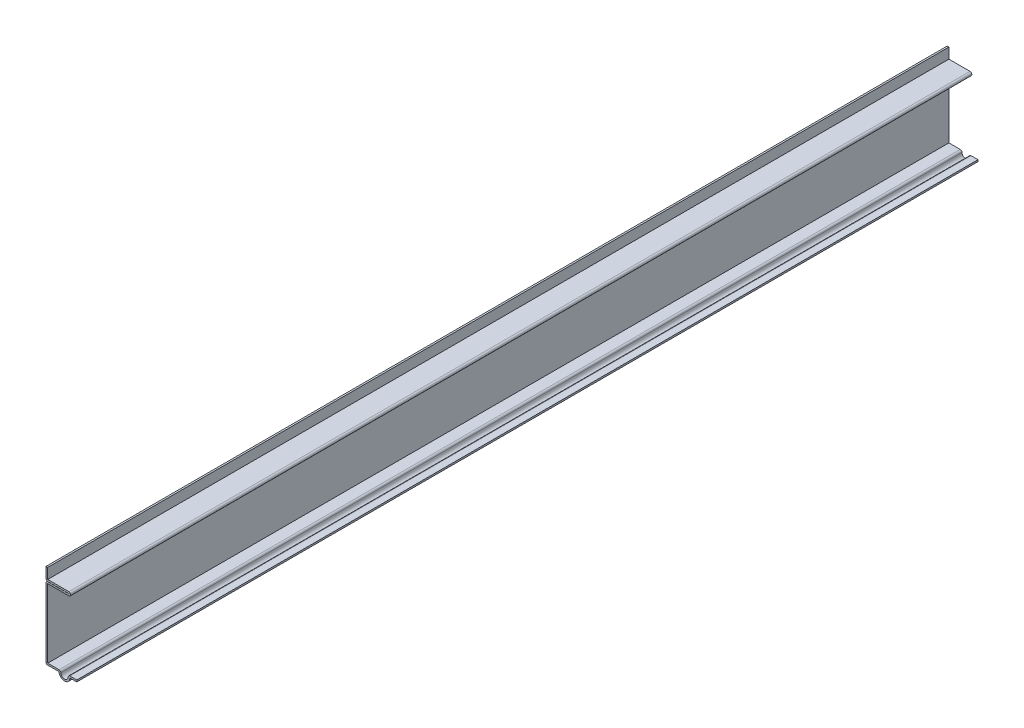
SolidWorks part; units mm, degrees
ref_plane "Front Plane" through (0, 0, 0) normal (0, 0, 1) x (1, 0, 0)
ref_plane "Top Plane" through (0, 0, 0) normal (0, 1, 0) x (1, 0, 0)
ref_plane "Right Plane" through (0, 0, 0) normal (1, 0, 0) x (0, 0, -1)
sketch "Sketch1" plane through (0, 0, 0) normal (0, 0, 1) x (1, 0, 0)
  line L0 (-15.875, 43.6562) -> (-15.875, 37.357)
  line L1 (-15.875, 37.357) -> (-4.1148, 37.357)
  line L2 (-4.1148, 37.2554) -> (-15.875, 37.2555)
  line L3 (-15.875, 37.2555) -> (-15.875, 0)
  line L4 (-15.875, 0) -> (-9.1281, 0)
  line L5 (-3.5719, 0) -> (0, 0)
  line L6 (-14.986, 43.6562) -> (-14.986, 38.246) construction
  line L7 (-14.986, 38.246) -> (-4.1148, 38.246) construction
  line L8 (-4.1148, 36.3665) -> (-14.986, 36.3665) construction
  line L9 (-14.986, 36.3665) -> (-14.986, 0.889) construction
  line L10 (-14.986, 0.889) -> (-8.0169, 0.889) construction
  line L11 (-4.6831, 0.889) -> (0, 0.889) construction
  arc A0 (-4.1148, 37.357) -> (-4.1148, 37.2554) centre (-4.1148, 37.3062) cw
  arc A1 (-9.1281, 0) -> (-3.5719, 0) centre (-6.35, 0) ccw
  arc A2 (-4.1148, 38.246) -> (-4.1148, 36.3665) centre (-4.1148, 37.3062) cw construction
  arc A3 (-8.0169, 0.889) -> (-4.6831, 0.889) centre (-6.35, 0) ccw construction
  point P11 (-9.4532, 0)
  dimension "D3" = 2.7781
  dimension "D6" = 0.0508
  dimension "D8" = 12.7
  dimension "D1" = 6.35
  dimension "D2" = 37.3062
  dimension "D4" = 15.875
  dimension "D5" = 9.525
  dimension "D7" = 0.889
extrude "Extrude-Thin1" add sketch "Sketch1" against normal blind 464.3438 thin thin type one direction reverse wall 0.889
fillet "Fillet1" radius 0.889 5 edges at (-15.875, 37.2555, -232.1719) (-15.875, 37.357, -232.1719) (-4.6831, 0.889, -232.1719) (-8.0169, 0.889, -232.1719) (-15.875, 0, -232.1719)
